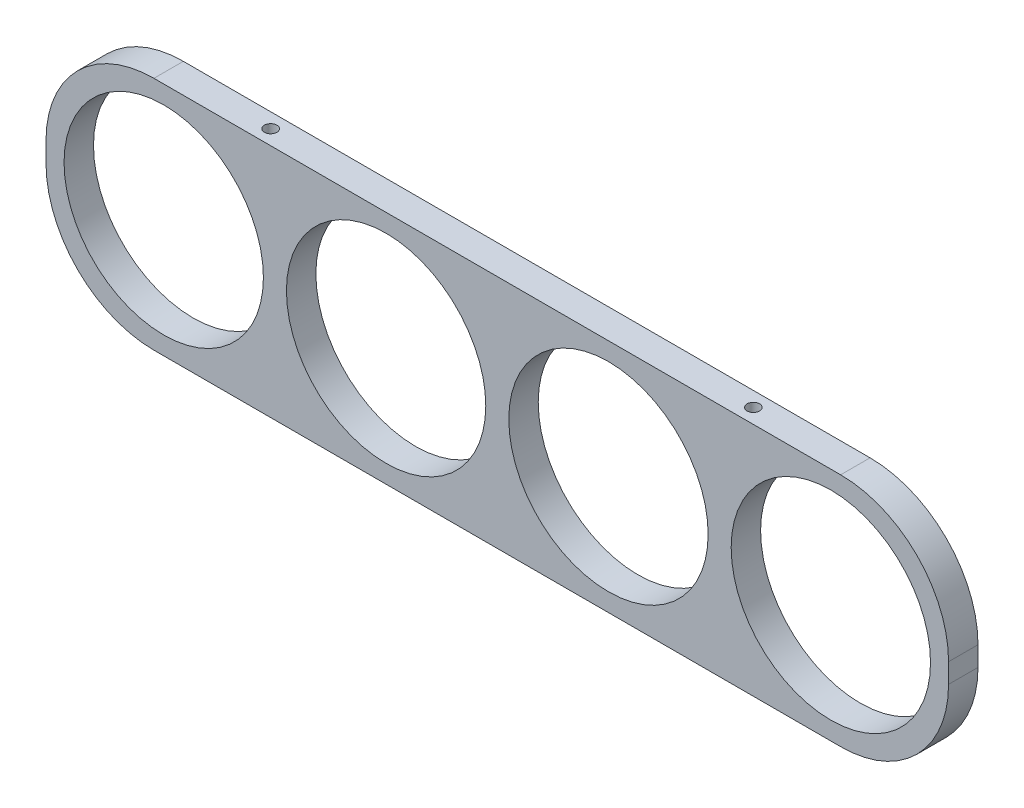
SolidWorks part; units mm, degrees
material "Delrin 2700 NC010, Low Viscosity Acetal Copolymer (SS)"
ref_plane "Front Plane" through (0, 0, 0) normal (0, 0, 1) x (1, 0, 0)
ref_plane "Top Plane" through (0, 0, 0) normal (0, 1, 0) x (1, 0, 0)
ref_plane "Right Plane" through (0, 0, 0) normal (1, 0, 0) x (0, 0, -1)
sketch "Sketch1" plane through (0, 0, 0) normal (0, 0, 1) x (1, 0, 0)
  line L1 (146.05, 38.1) -> (-146.05, 38.1)
  line L2 (146.05, 38.1) -> (146.05, -38.1)
  line L3 (146.05, -38.1) -> (-146.05, -38.1)
  line L4 (-146.05, 38.1) -> (-146.05, -38.1)
  line L5 (146.05, 38.1) -> (-146.05, -38.1) construction
  line L6 (146.05, -38.1) -> (-146.05, 38.1) construction
  point P0 (0, 0)
  dimension "D1" = 292.1
  dimension "D2" = 76.2
extrude "Boss-Extrude1" add sketch "Sketch1" along normal mid plane 9.525
sketch "Sketch2" plane through (0, 0, 4.7625) normal (0, 0, 1) x (1, 0, 0)
  line L0 (-107.95, 0) -> (-35.9833, 0) construction
  line L1 (-35.9833, 0) -> (35.9833, 0) construction
  line L2 (35.9833, 0) -> (107.95, 0) construction
  line L4 (-146.05, 38.1) -> (-146.05, -38.1) construction
  circle A0 centre (-107.95, 0) radius 32.258
  circle A1 centre (-35.9833, 0) radius 32.258
  circle A2 centre (35.9833, 0) radius 32.258
  circle A3 centre (107.95, 0) radius 32.258
  dimension "D1" = 64.516
  dimension "D2" = 38.1
extrude "Cut-Extrude1" cut sketch "Sketch2" against normal through all
fillet "Fillet1" radius 34.925 4 edges at (-146.05, 38.1, 0) (146.05, -38.1, 0) (-146.05, -38.1, 0) (146.05, 38.1, 0)
hole_wizard "#10-32 Tapped Hole2" positions "Sketch6" profile "Sketch7" tap size "#10-32" standard "ANSI Inch"
sketch "Sketch6" plane through (0, 38.1, 0) normal (0, 1, 0) x (1, 0, 0)
  line L0 (-78.105, 0) -> (78.105, 0) construction
  point P0 (-78.105, 0)
  point P2 (78.105, 0)
  dimension "D1" = 156.21
sketch "Sketch7" plane through (-78.105, 38.1, 0) normal (1, 0, 0) x (0, 0, 1)
  line L0 (0, 0) -> (0, 20.2633)
  line L1 (0, 20.2633) -> (2.0193, 19.05)
  line L2 (2.0193, 19.05) -> (2.0193, 0)
  line L5 (2.0193, 0) -> (0, 0)
  line L10 (0, 20.2633) -> (-2.0193, 19.05) construction
  line L11 (0, -6.35) -> (0, 107.95) construction
  dimension "Tap Drill Dia." = 4.0386
  dimension "Tap Drill Depth" = 19.05
  dimension "Drill Angle" = 118
cosmetic thread "Hole Thread5" parameters "D1"=9.652, "D2"=4.826
cosmetic thread "Hole Thread6" parameters "D1"=9.652, "D2"=4.826
